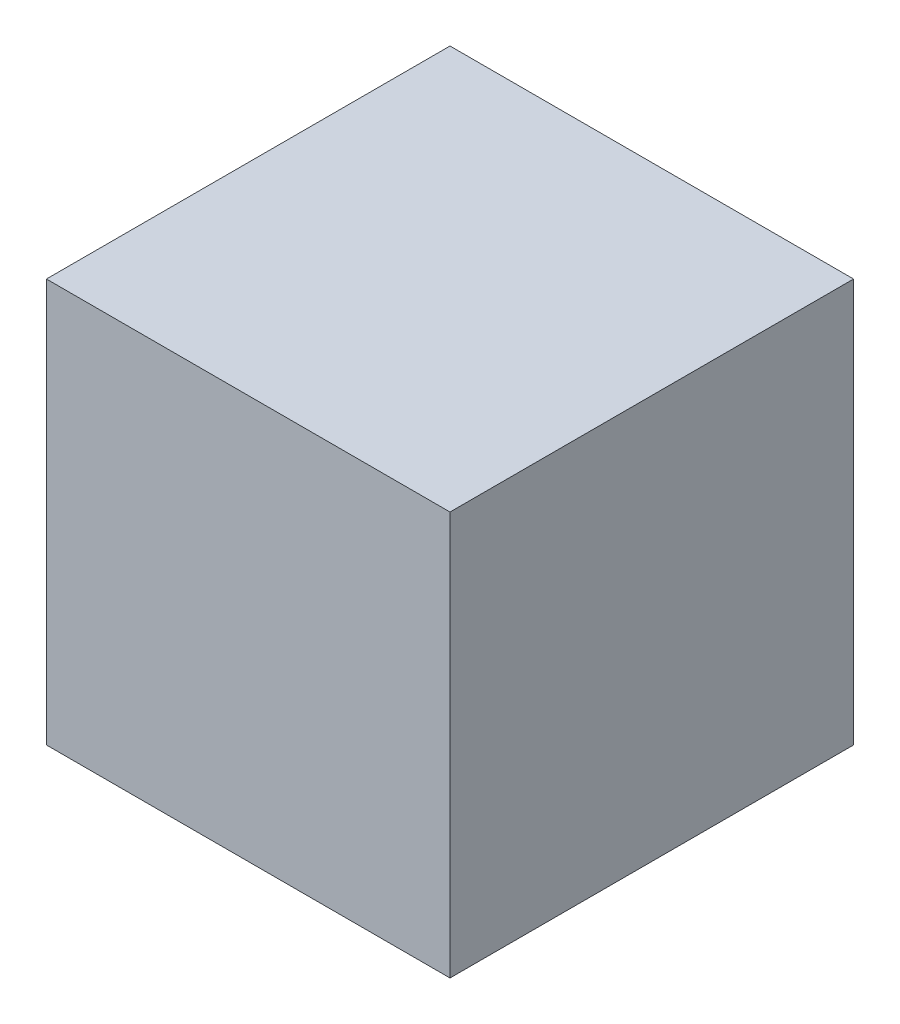
SolidWorks part; units mm, degrees
ref_plane "Front Plane" through (0, 0, 0) normal (0, 0, 1) x (1, 0, 0)
ref_plane "Top Plane" through (0, 0, 0) normal (0, 1, 0) x (1, 0, 0)
ref_plane "Right Plane" through (0, 0, 0) normal (1, 0, 0) x (0, 0, -1)
sketch "Sketch1" plane through (0, 0, 0) normal (0, 1, 0) x (1, 0, 0)
  line L1 (-40, -40) -> (40, -40)
  line L2 (-40, -40) -> (-40, 40)
  line L3 (-40, 40) -> (40, 40)
  line L4 (40, -40) -> (40, 40)
  line L5 (-40, -40) -> (40, 40) construction
  line L6 (-40, 40) -> (40, -40) construction
  point P0 (0, 0)
  dimension "D1" = 80
  dimension "D2" = 80
extrude "Boss-Extrude1" add sketch "Sketch1" along normal blind 80
